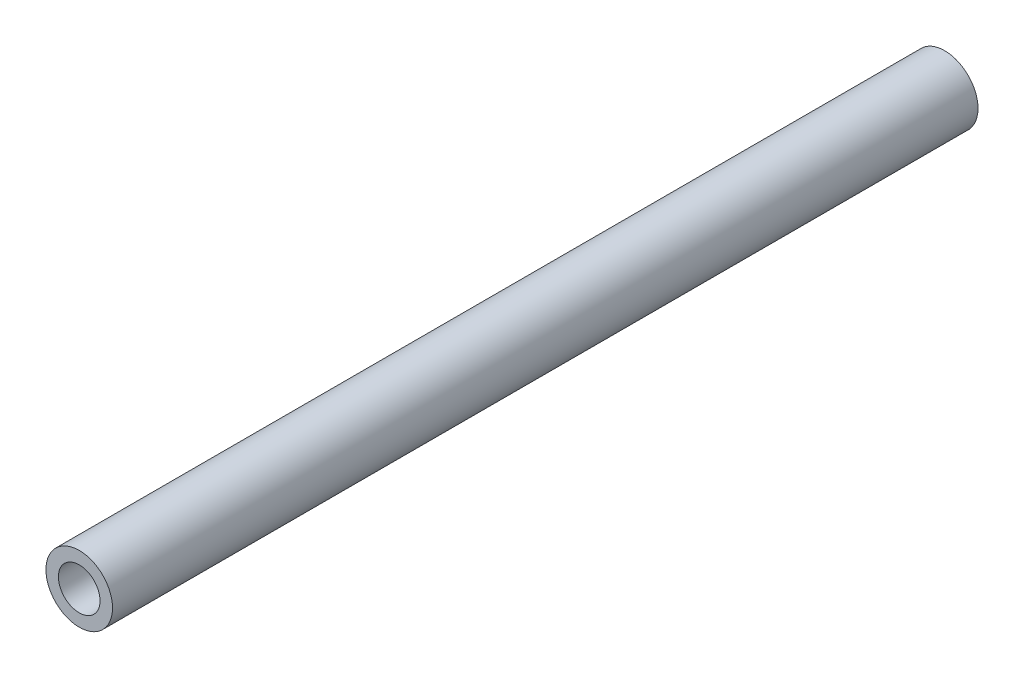
SolidWorks part; units mm, degrees
material "6061 Alloy"
ref_plane "Front Plane" through (0, 0, 0) normal (0, 0, 1) x (1, 0, 0)
ref_plane "Top Plane" through (0, 0, 0) normal (0, 1, 0) x (1, 0, 0)
ref_plane "Right Plane" through (0, 0, 0) normal (1, 0, 0) x (0, 0, -1)
sketch "Sketch1" plane through (0, 0, 0) normal (0, 0, 1) x (1, 0, 0)
  circle A0 centre (0, 0) radius 4
  circle A1 centre (0, 0) radius 2.5
  dimension "D1" = 8
  dimension "D2" = 5
extrude "Boss-Extrude1" add sketch "Sketch1" along normal blind 104
